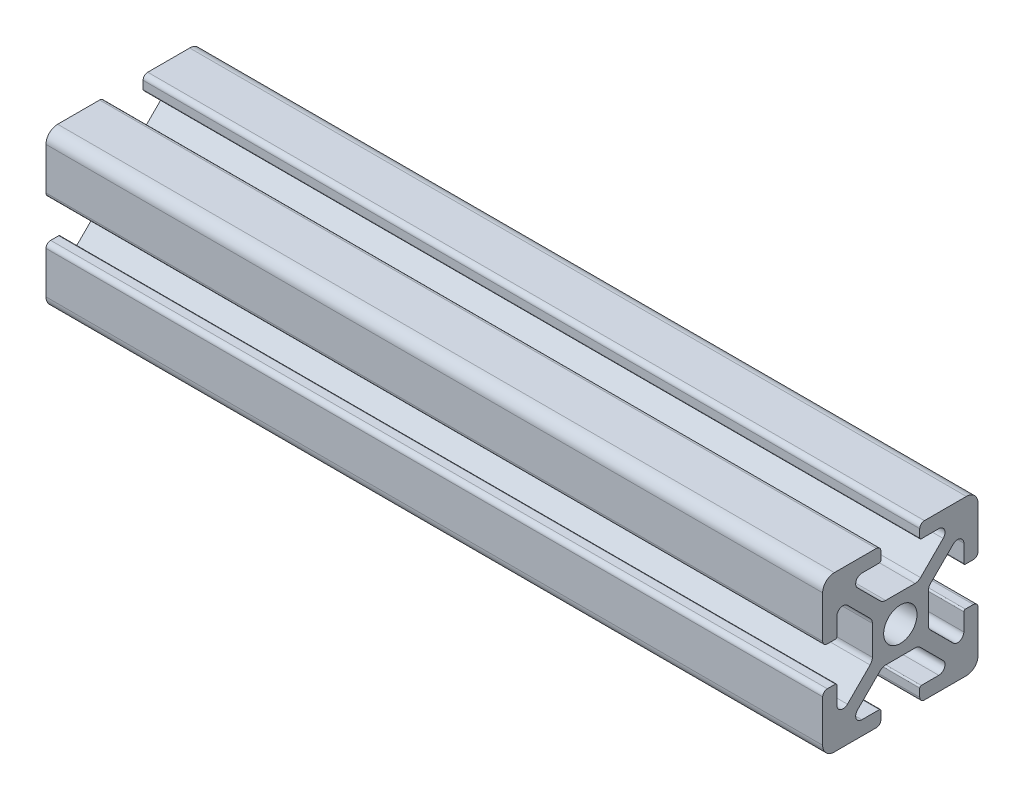
SolidWorks part; units mm, degrees
ref_plane "Front Plane" through (0, 0, 0) normal (0, 0, 1) x (1, 0, 0)
ref_plane "Top Plane" through (0, 0, 0) normal (0, 1, 0) x (1, 0, 0)
ref_plane "Right Plane" through (0, 0, 0) normal (1, 0, 0) x (0, 0, -1)
sketch "Sketch1" plane through (0, 0, 0) normal (1, 0, 0) x (0, 0, -1)
  line L0 (0, -10) -> (0, 10) construction
  line L1 (10, -10) -> (-10, -10)
  line L2 (10, -10) -> (10, 10)
  line L3 (10, 10) -> (0, 10)
  line L4 (-10, -10) -> (-10, 10)
  line L5 (10, -10) -> (-10, 10) construction
  line L6 (10, 10) -> (-10, -10) construction
  line L7 (10, 0) -> (-10, 0) construction
  line L8 (-2.5, 9.4) -> (-2.5, 8.3731)
  line L9 (-2.7, 8.1731) -> (-4.95, 8.1731)
  line L10 (-5.5157, 6.8075) -> (-2.6011, 3.8929)
  line L11 (-1.894, 3.6) -> (0, 3.6)
  line L12 (-5.3502, 4.0584) -> (-4.0584, 5.3502) construction
  line L13 (-3.825, 8.1731) -> (-3.825, 10) construction
  line L14 (-3.1, 10) -> (-10, 10)
  line L15 (-5.75, 7.3731) -> (5.75, 7.3731) construction
  circle A0 centre (0, 0) radius 2.15
  arc A1 (-4.95, 8.1731) -> (-5.5157, 6.8075) centre (-4.95, 7.3731) ccw
  arc A2 (-2.6011, 3.8929) -> (-1.894, 3.6) centre (-1.894, 4.6) ccw
  arc A3 (-2.5, 8.3731) -> (-2.7, 8.1731) centre (-2.7, 8.3731) cw
  arc A4 (-2.5, 9.4) -> (-3.1, 10) centre (-3.1, 9.4) ccw
  point P0 (0, 0)
  point P9 (0, 0)
  point P12 (0, 0)
  point P22 (-4.7043, 4.7043)
  point P32 (-2.5, 10)
  point P33 (-2.5, 8.8866)
  point P35 (-4.0584, 5.3502)
  point P37 (0, 7.3731)
  dimension "Center Hole Diameter" = 4.3
  dimension "D4" = 1
  dimension "D5" = 0.2
  dimension "D6" = 0.6
  dimension "D3" = 0.8
  dimension "Rail Height" = 20
  dimension "D7" = 6.4
  dimension "T Slot Width" = 5
  dimension "D10" = 10
  dimension "Rail Width" = 20
  dimension "D2" = 11.5
sketch "Sketch2" plane through (0, 0, 0) normal (0, 0, 1) x (1, 0, 0)
  line L0 (-132.4, 10) -> (-132.4, -10) construction
  line L1 (152.4, -10) -> (-152.4, -10) construction
  line L2 (152.4, -10) -> (152.4, 10) construction
  line L3 (152.4, 10) -> (-152.4, 10) construction
  line L4 (-152.4, -10) -> (-152.4, 10) construction
  line L5 (152.4, -10) -> (-152.4, 10) construction
  line L6 (152.4, 10) -> (-152.4, -10) construction
  line L7 (132.4, 10) -> (132.4, -10) construction
  point P0 (0, 0)
  point P12 (132.4, 0)
  dimension "Length" = 304.8
  dimension "D1" = 20
  dimension "D2" = 20
sketch "Sketch3" plane through (0, 0, 0) normal (1, 0, 0) x (0, 0, -1)
  line L0 (-5.5157, 6.8075) -> (-2.6011, 3.8929) construction
  line L5 (-3.1, 10) -> (-10, 10) construction
  line L6 (-2.5, 9.4) -> (-2.5, 8.3731) construction
  line L7 (-2.7, 8.1731) -> (-4.95, 8.1731) construction
  line L8 (-1.894, 3.6) -> (0, 3.6) construction
  line L9 (-5.5157, 6.8075) -> (-2.6011, 3.8929)
  line L10 (-10, 10) -> (0, 0) construction
  line L12 (-3.6, 1.894) -> (-3.6, 0)
  line L13 (-8.1731, 2.7) -> (-8.1731, 4.95)
  line L14 (-3.1, 10) -> (-8.5, 10)
  line L15 (-2.5, 9.4) -> (-2.5, 8.3731)
  line L16 (-2.7, 8.1731) -> (-4.95, 8.1731)
  line L17 (-1.894, 3.6) -> (0, 3.6)
  line L18 (-9.4, 2.5) -> (-8.3731, 2.5)
  line L19 (-10, 3.1) -> (-10, 8.5)
  line L20 (-6.8075, 5.5157) -> (-3.8929, 2.6011)
  line L21 (-3.6, 0) -> (-2.15, 0)
  line L22 (0, 3.6) -> (0, 2.15)
  arc A0 (-2.5, 9.4) -> (-3.1, 10) centre (-3.1, 9.4) ccw construction
  arc A1 (-2.7, 8.1731) -> (-2.5, 8.3731) centre (-2.7, 8.3731) ccw construction
  arc A2 (-4.95, 8.1731) -> (-5.5157, 6.8075) centre (-4.95, 7.3731) ccw construction
  arc A3 (-2.6011, 3.8929) -> (-1.894, 3.6) centre (-1.894, 4.6) ccw construction
  arc A4 (-2.5, 9.4) -> (-3.1, 10) centre (-3.1, 9.4) ccw
  arc A5 (-2.7, 8.1731) -> (-2.5, 8.3731) centre (-2.7, 8.3731) ccw
  arc A6 (-4.95, 8.1731) -> (-5.5157, 6.8075) centre (-4.95, 7.3731) ccw
  arc A7 (-2.6011, 3.8929) -> (-1.894, 3.6) centre (-1.894, 4.6) ccw
  arc A8 (-3.8929, 2.6011) -> (-3.6, 1.894) centre (-4.6, 1.894) cw
  arc A9 (-8.1731, 4.95) -> (-6.8075, 5.5157) centre (-7.3731, 4.95) cw
  arc A10 (-8.1731, 2.7) -> (-8.3731, 2.5) centre (-8.3731, 2.7) cw
  arc A11 (-9.4, 2.5) -> (-10, 3.1) centre (-9.4, 3.1) cw
  circle A12 centre (0, 0) radius 2.15 construction
  arc A13 (0, 2.15) -> (-2.15, 0) centre (0, 0) ccw
  arc A14 (-10, 8.5) -> (-8.5, 10) centre (-8.5, 8.5) cw
  dimension "D1" = 1.5
extrude "Boss-Extrude1" add sketch "Sketch3" against normal blind 100
mirror "Mirror1" about plane through (0, 0, 0) normal (0, 1, 0) of bodies 104
mirror "Mirror2" about plane through (0, 0, 0) normal (0, 0, 1) of bodies 105
equation "\"D10@Sketch1\" = \"Rail Height@Sketch1\" / 2"
equation "\"D2@Sketch2\"=\"D1@Sketch2\""
